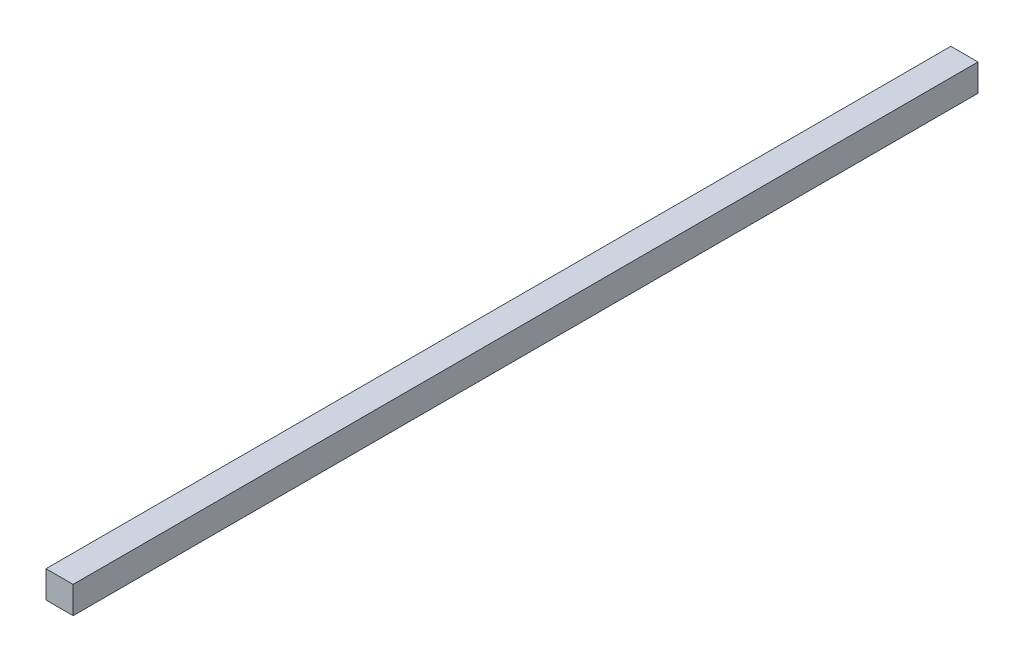
SolidWorks part; units mm, degrees
ref_plane "前视基准面" through (0, 0, 0) normal (0, 0, 1) x (1, 0, 0)
ref_plane "上视基准面" through (0, 0, 0) normal (0, 1, 0) x (1, 0, 0)
ref_plane "右视基准面" through (0, 0, 0) normal (1, 0, 0) x (0, 0, -1)
other "Configuration Table"
sketch "草图1" plane through (0, 0, 0) normal (0, 0, 1) x (1, 0, 0)
  line L1 (0, 0) -> (3, 0)
  line L2 (0, 0) -> (0, 3)
  line L3 (0, 3) -> (3, 3)
  line L4 (3, 0) -> (3, 3)
  dimension "D1" = 3
  dimension "D2" = 3
extrude "凸台-拉伸1" add sketch "草图1" along normal blind 100
